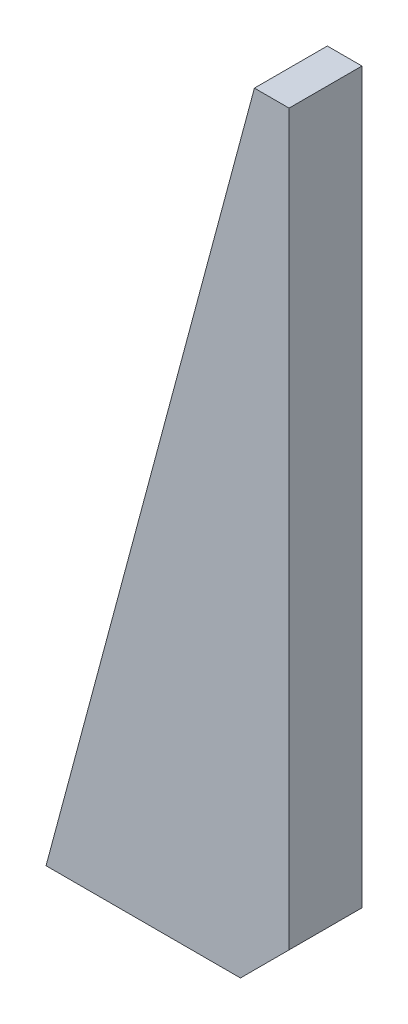
SolidWorks part; units mm, degrees
ref_plane "Front" through (0, 0, 0) normal (0, 0, 1) x (1, 0, 0)
ref_plane "Top" through (0, 0, 0) normal (0, 1, 0) x (1, 0, 0)
ref_plane "Right" through (0, 0, 0) normal (1, 0, 0) x (0, 0, -1)
sketch "Sketch1" plane through (0, 0, 0) normal (0, 0, 1) x (1, 0, 0)
  line L0 (0, 0) -> (-42.8719, -160)
  line L1 (-42.8719, -160) -> (7.1281, -160)
  line L2 (7.1281, -160) -> (7.1281, 0)
  line L3 (7.1281, 0) -> (0, 0)
  dimension "D1" = 75
  dimension "D2" = 50
  dimension "D3" = 160
extrude "Boss-Extrude1" add sketch "Sketch1" along normal blind 15
chamfer "Chamfer1" distance 10 angle 45 1 edges at (7.1281, -160, 7.5)
